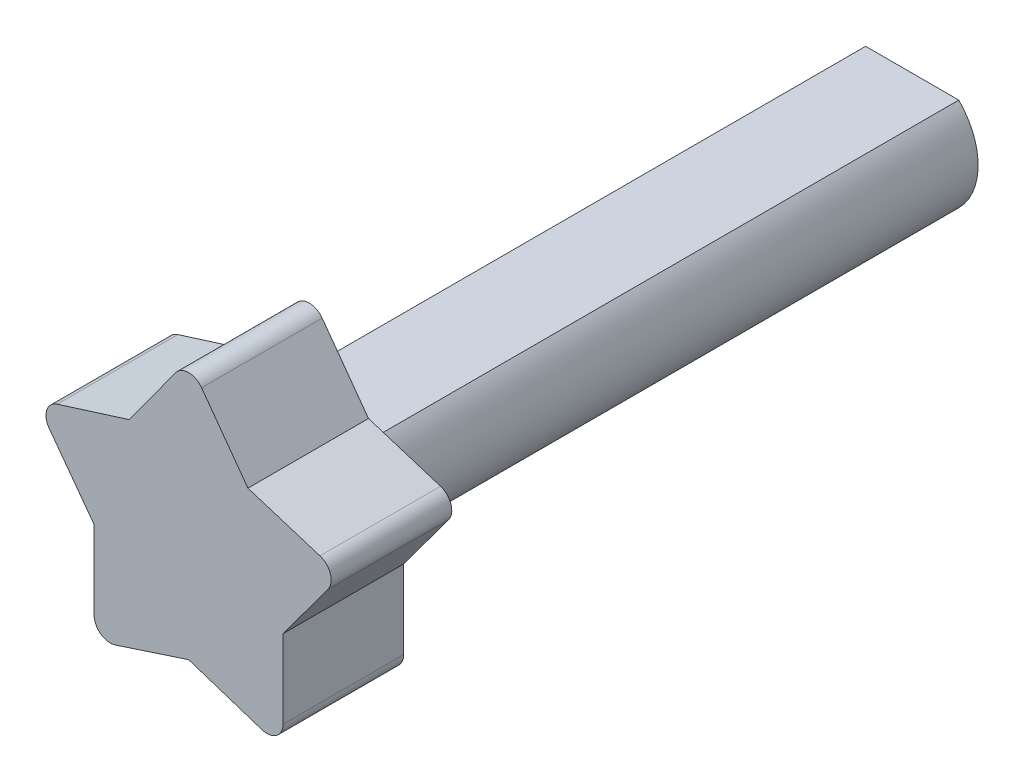
SolidWorks part; units mm, degrees
ref_plane "Front Plane" through (0, 0, 0) normal (0, 0, 1) x (1, 0, 0)
ref_plane "Top Plane" through (0, 0, 0) normal (0, 1, 0) x (1, 0, 0)
ref_plane "Right Plane" through (0, 0, 0) normal (1, 0, 0) x (0, 0, -1)
sketch "Sketch1" plane through (0, 0, 0) normal (0, 0, 1) x (1, 0, 0)
  line L0 (-7.3411, -7.3022) -> (7.3778, -7.3022)
  line L1 (-7.3411, 7.4341) -> (7.3778, 7.4341)
  arc A0 (-7.3411, 7.4341) -> (-7.3411, -7.3022) centre (0.0184, 0.0659) ccw
  arc A1 (7.3778, -7.3022) -> (7.3778, 7.4341) centre (0.0184, 0.0659) ccw
extrude "Boss-Extrude1" add sketch "Sketch1" against normal blind 114.3
sketch "Sketch2" plane through (0, 0, 0) normal (0, 0, 1) x (1, 0, 0)
  line L0 (0, 0) -> (0, 25.3905)
  line L5 (-11.5948, -19.4528) -> (0, -15.6618)
  line L6 (-14.9242, -17.0386) -> (-14.9242, -4.642)
  line L7 (11.5948, -19.4528) -> (0, -15.6618)
  line L8 (14.9242, -17.0386) -> (14.9242, -4.642)
  line L9 (-22.0321, 4.9816) -> (-14.9242, -4.642)
  line L10 (-20.7505, 8.9138) -> (-9.3732, 12.4894)
  line L11 (-2.0549, 22.5622) -> (-9.3732, 12.4894)
  line L12 (2.0549, 22.5622) -> (9.3732, 12.4894)
  line L13 (20.7505, 8.9138) -> (9.3732, 12.4894)
  line L14 (22.0321, 4.9816) -> (14.9242, -4.642)
  arc A2 (-22.0321, 4.9816) -> (-20.7505, 8.9138) centre (-19.989, 6.4906) cw
  arc A3 (2.0549, 22.5622) -> (-2.0549, 22.5622) centre (0, 21.0692) ccw
  arc A4 (22.0321, 4.9816) -> (20.7505, 8.9138) centre (19.989, 6.4906) ccw
  arc A5 (11.5948, -19.4528) -> (14.9242, -17.0386) centre (12.3842, -17.0386) ccw
  arc A6 (-14.9242, -17.0386) -> (-11.5948, -19.4528) centre (-12.3842, -17.0386) ccw
  point P13 (-24.1478, 7.8461)
  point P21 (24.1478, 7.8461)
  point P24 (14.9242, -20.5414)
  point P27 (-14.9242, -20.5414)
  dimension "D1" = 2.54
  dimension "D2" = 2.54
  dimension "D3" = 2.54
  dimension "D4" = 2.54
  dimension "D5" = 2.54
extrude "Boss-Extrude2" add sketch "Sketch2" against normal blind 19.05
